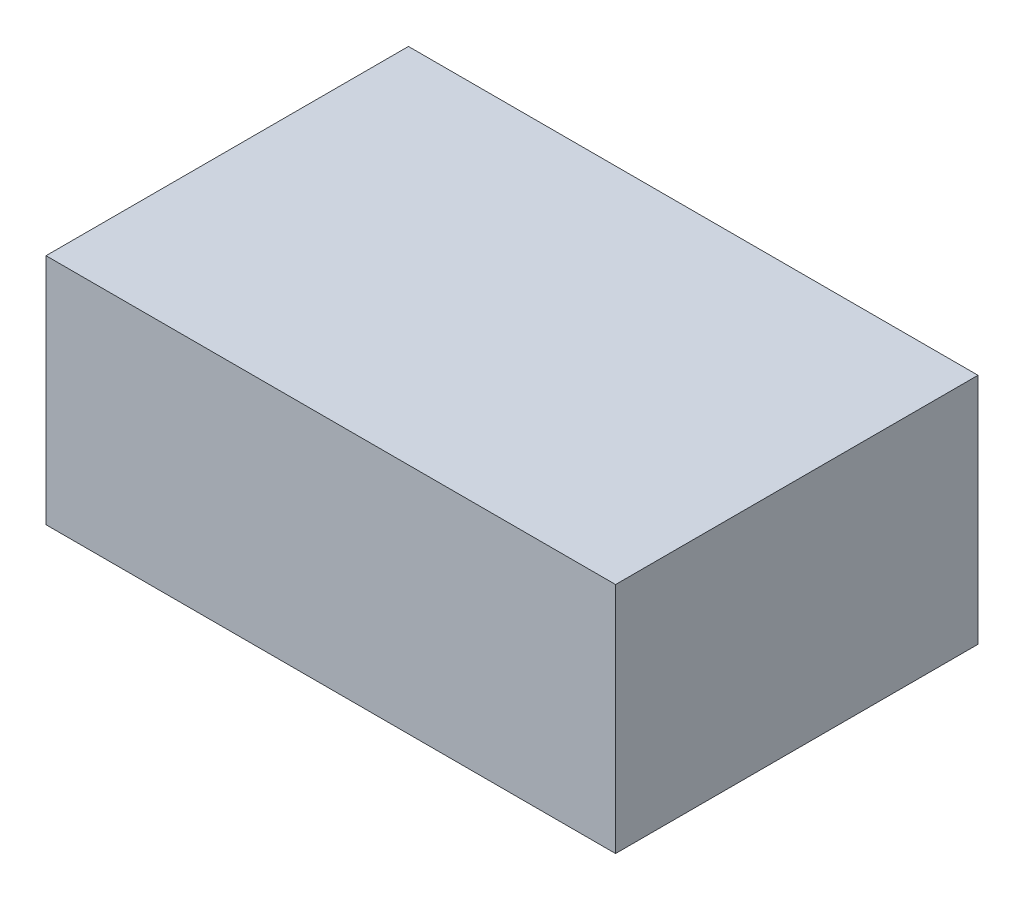
SolidWorks part; units mm, degrees
ref_plane "Front Plane" through (0, 0, 0) normal (0, 0, 1) x (1, 0, 0)
ref_plane "Top Plane" through (0, 0, 0) normal (0, 1, 0) x (1, 0, 0)
ref_plane "Right Plane" through (0, 0, 0) normal (1, 0, 0) x (0, 0, -1)
sketch "Sketch1" plane through (0, 0, 0) normal (0, 1, 0) x (1, 0, 0)
  line L1 (-34.925, -22.225) -> (34.925, -22.225)
  line L2 (-34.925, -22.225) -> (-34.925, 22.225)
  line L3 (-34.925, 22.225) -> (34.925, 22.225)
  line L4 (34.925, -22.225) -> (34.925, 22.225)
  line L5 (-34.925, -22.225) -> (34.925, 22.225) construction
  line L6 (-34.925, 22.225) -> (34.925, -22.225) construction
  point P0 (0, 0)
  dimension "D1" = 69.85
  dimension "D2" = 44.45
extrude "Boss-Extrude1" add sketch "Sketch1" along normal blind 28.575
